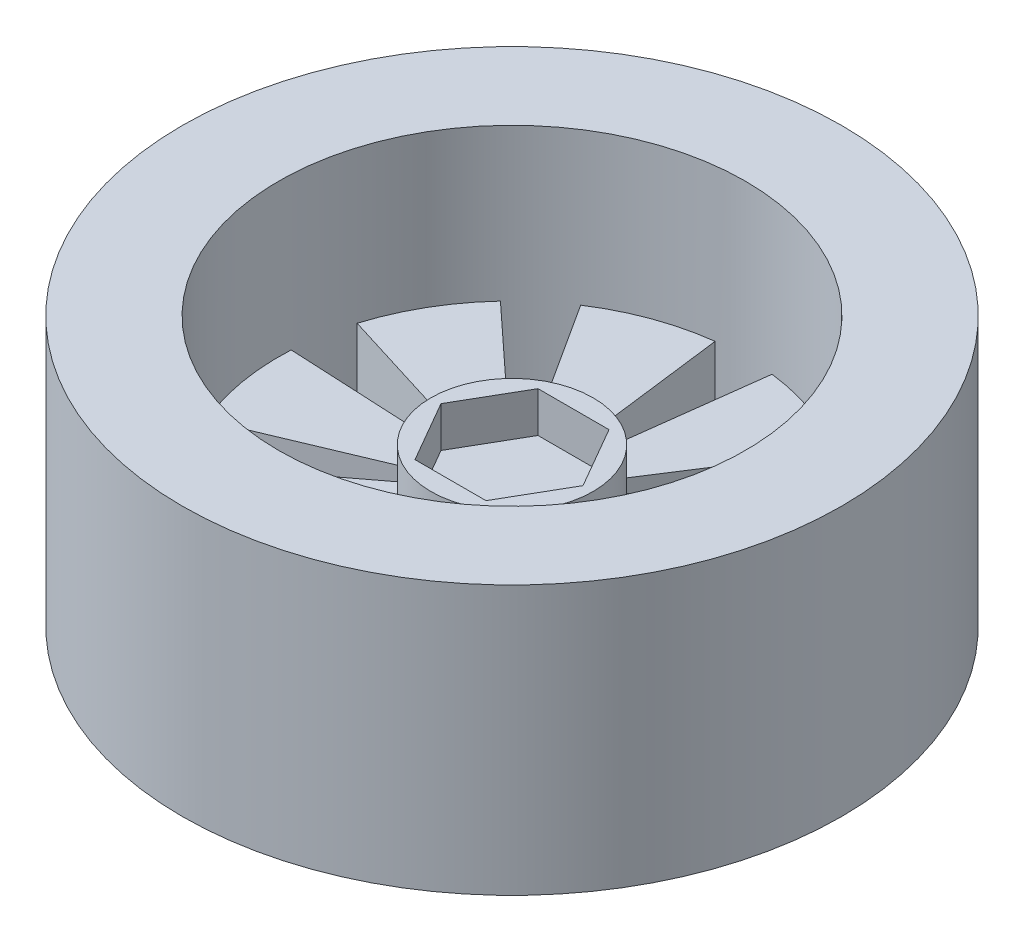
SolidWorks part; units mm, degrees
ref_plane "前视基准面" through (0, 0, 0) normal (0, 0, 1) x (1, 0, 0)
ref_plane "上视基准面" through (0, 0, 0) normal (0, 1, 0) x (1, 0, 0)
ref_plane "右视基准面" through (0, 0, 0) normal (1, 0, 0) x (0, 0, -1)
sketch "草图1" plane through (0, 0, 0) normal (0, 0, 1) x (1, 0, 0)
  line L0 (0, 54.3812) -> (0, -63.8201) construction
  line L1 (0, 0) -> (32.5, 0)
  line L2 (32.5, 0) -> (32.5, 26.5)
  line L3 (32.5, 26.5) -> (0, 26.5)
  line L4 (0, 0) -> (0, 26.5)
  dimension "D1" = 32.5
  dimension "D2" = 26.5
revolve "旋转1" add sketch "草图1" angle 360 about L0
sketch "草图2" plane through (0, 26.5, 0) normal (0, 1, 0) x (1, 0, 0)
  circle A0 centre (0, 0) radius 23
  dimension "D1" = 46
extrude "切除-拉伸1" cut sketch "草图2" against normal blind 15
sketch "草图3" plane through (0, 11.5, 0) normal (0, 1, 0) x (1, 0, 0)
  line L0 (-11.4604, 0) -> (10.17, 0) construction
  line L1 (0, 12.6376) -> (0, -10.223) construction
  line L2 (-3.5, 6.0622) -> (3.5, 6.0622)
  line L3 (3.5, 6.0622) -> (7, 0)
  line L4 (3.5, -6.0622) -> (7, 0)
  line L5 (-3.5, -6.0622) -> (3.5, -6.0622)
  line L6 (-3.5, -6.0622) -> (-7, 0)
  line L7 (-3.5, 6.0622) -> (-7, 0)
  circle A0 centre (0, 0) radius 8
  point P13 (0, -6.0622)
  point P15 (0, 6.0622)
  dimension "D1" = 16
  dimension "D2" = 3.5
  dimension "D3" = 7
  dimension "D4" = 120
extrude "凸台-拉伸1" add sketch "草图3" along normal blind 4
sketch "草图4" plane through (0, 11.5, 0) normal (0, 1, 0) x (1, 0, 0)
  line L0 (0, 23) -> (0, -23) construction
  line L1 (-23, 0) -> (23, 0) construction
  line L2 (-0.9253, 7.9463) -> (-2.8077, 22.828)
  line L3 (0.9253, 7.9463) -> (2.8077, 22.828)
  line L4 (5.8166, 5.4925) -> (16.8244, 15.6825)
  line L5 (4.399, 6.682) -> (12.5227, 19.292)
  line L6 (7.9863, 0.4687) -> (22.9687, 1.199)
  line L7 (7.6649, 2.2911) -> (21.9936, 6.7291)
  line L8 (6.4191, -4.7744) -> (18.3658, -13.8455)
  line L9 (7.3443, -3.1719) -> (21.1735, -8.9824)
  line L10 (1.8483, -7.7835) -> (5.1692, -22.4116)
  line L11 (3.5873, -7.1506) -> (10.446, -20.491)
  line L12 (-3.5873, -7.1506) -> (-10.446, -20.491)
  line L13 (-1.8483, -7.7835) -> (-5.1692, -22.4116)
  line L14 (-7.3443, -3.1719) -> (-21.1735, -8.9824)
  line L15 (-6.4191, -4.7744) -> (-18.3658, -13.8455)
  line L16 (-7.6649, 2.2911) -> (-21.9936, 6.7291)
  line L17 (-7.9863, 0.4687) -> (-22.9687, 1.199)
  line L18 (-4.399, 6.682) -> (-12.5227, 19.292)
  line L19 (-5.8166, 5.4925) -> (-16.8244, 15.6825)
  circle A0 centre (0, 0) radius 23 construction
  circle A1 centre (0, 0) radius 23 construction
  circle A2 centre (0, 0) radius 8 construction
  arc A5 (2.8077, 22.828) -> (-2.8077, 22.828) centre (0, 0) ccw
  arc A6 (0.9253, 7.9463) -> (-0.9253, 7.9463) centre (0, 0) ccw
  arc A7 (16.8244, 15.6825) -> (12.5227, 19.292) centre (0, 0) ccw
  arc A8 (5.8166, 5.4925) -> (4.399, 6.682) centre (0, 0) ccw
  arc A9 (22.9687, 1.199) -> (21.9936, 6.7291) centre (0, 0) ccw
  arc A10 (7.9863, 0.4687) -> (7.6649, 2.2911) centre (0, 0) ccw
  arc A11 (18.3658, -13.8455) -> (21.1735, -8.9824) centre (0, 0) ccw
  arc A12 (6.4191, -4.7744) -> (7.3443, -3.1719) centre (0, 0) ccw
  arc A13 (5.1692, -22.4116) -> (10.446, -20.491) centre (0, 0) ccw
  arc A14 (1.8483, -7.7835) -> (3.5873, -7.1506) centre (0, 0) ccw
  arc A15 (-10.446, -20.491) -> (-5.1692, -22.4116) centre (0, 0) ccw
  arc A16 (-3.5873, -7.1506) -> (-1.8483, -7.7835) centre (0, 0) ccw
  arc A17 (-21.1735, -8.9824) -> (-18.3658, -13.8455) centre (0, 0) ccw
  arc A18 (-7.3443, -3.1719) -> (-6.4191, -4.7744) centre (0, 0) ccw
  arc A19 (-21.9936, 6.7291) -> (-22.9687, 1.199) centre (0, 0) ccw
  arc A20 (-7.6649, 2.2911) -> (-7.9863, 0.4687) centre (0, 0) ccw
  arc A21 (-12.5227, 19.292) -> (-16.8244, 15.6825) centre (0, 0) ccw
  arc A22 (-4.399, 6.682) -> (-5.8166, 5.4925) centre (0, 0) ccw
  point P52 (0, 0)
  dimension "D1" = 9
extrude "切除-拉伸2" cut sketch "草图4" against normal through all
